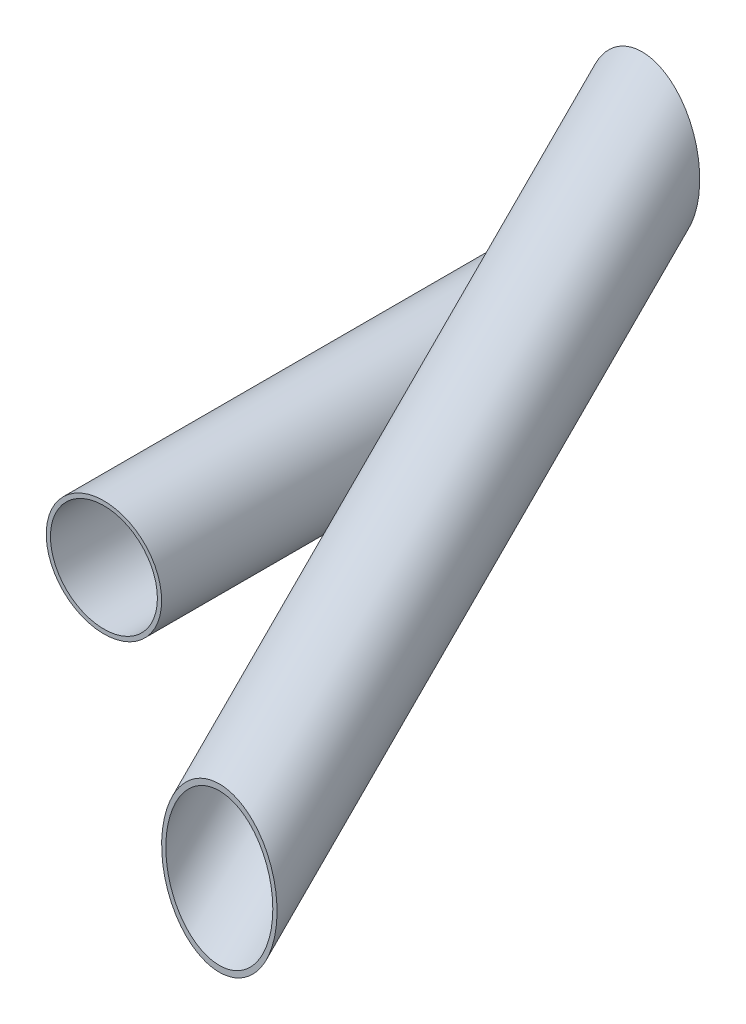
SolidWorks part; units mm, degrees
ref_plane "Plan de face" through (0, 0, 0) normal (0, 0, 1) x (1, 0, 0)
ref_plane "Plan de dessus" through (0, 0, 0) normal (0, 1, 0) x (1, 0, 0)
ref_plane "Plan de droite" through (0, 0, 0) normal (1, 0, 0) x (0, 0, -1)
sketch "Esquisse1" plane through (0, 0, 0) normal (0, 0, 1) x (1, 0, 0)
  line L0 (0, 0) -> (59.7743, 0) construction
  line L1 (0, 0) -> (-29.8872, -51.7661) construction
  line L2 (0, 0) -> (-29.8872, 51.7661) construction
  circle A0 centre (0, 0) radius 12.65
  circle A1 centre (0, 0) radius 13.65
  point P9 (0, 0)
  dimension "D2" = 25.3
  dimension "D3" = 27.3
  dimension "D1" = 3
extrude "Boss.-Extru.1" add sketch "Esquisse1" along normal mid plane 100
ref_plane "Plan1" through (0, 0, 0) normal (0, -0.7071, 0.7071) x (1, 0, 0)
sketch "Esquisse15" plane through (0, 0, 0) normal (0, -0.7071, 0.7071) x (1, 0, 0)
  circle A6 centre (27.3, 0) radius 12.65
  circle A7 centre (27.3, 0) radius 13.65
  ellipse E1 centre (0, 0) end of major axis (13.65, 0) minor radius 9.652 construction
  point P2 (27.4018, 0)
  dimension "D1" = 25.3
  dimension "D2" = 27.3
extrude "Boss.-Extru.6" add sketch "Esquisse15" along normal up to surface and the other way up to surface separate body up to face at (13.65, 0, 50) other way up to face at (13.65, 0, -50)
equation "\"diam_int_eq\"= 25.3"
equation "\"D2@Esquisse1\"=\"diam_int_eq\""
equation "\"D3@Esquisse1\"=\"diam_ext_eq\""
equation "\"D1@Esquisse5\"=\"diam_int_eq\""
equation "\"D2@Esquisse5\"=\"diam_ext_eq\""
equation "\"diam_ext_eq\"= \"diam_int_eq\" + 2"
equation "\"D1@Esquisse15\"=\"diam_int_eq\""
equation "\"D2@Esquisse15\"=\"diam_ext_eq\""
